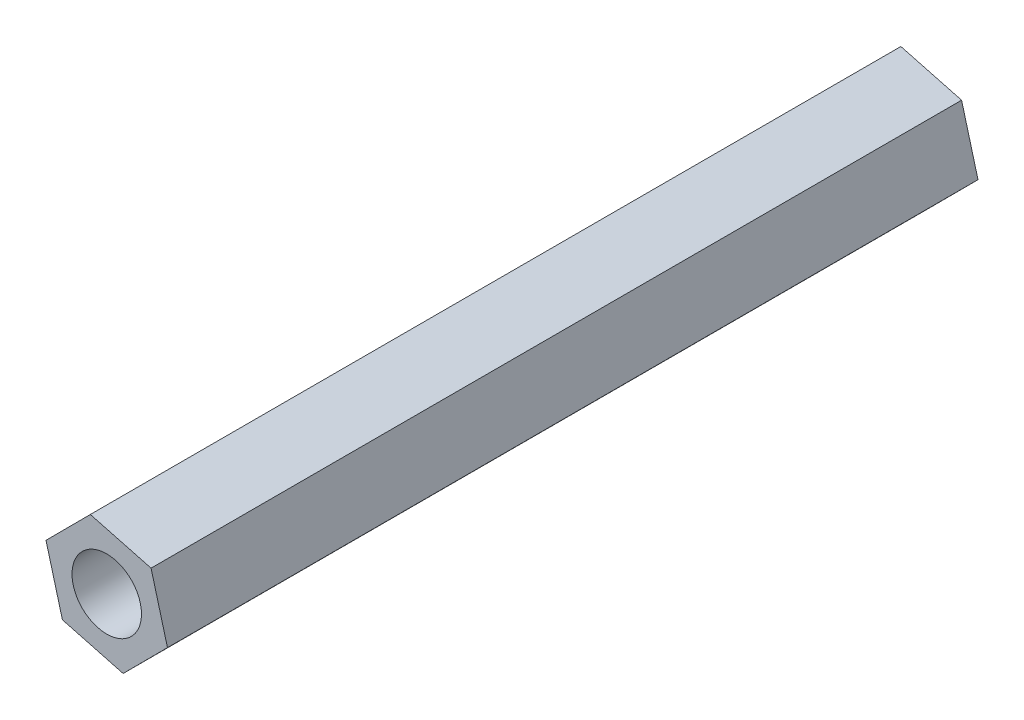
SolidWorks part; units mm, degrees
ref_plane "Front Plane" through (0, 0, 0) normal (0, 0, 1) x (1, 0, 0)
ref_plane "Top Plane" through (0, 0, 0) normal (0, 1, 0) x (1, 0, 0)
ref_plane "Right Plane" through (0, 0, 0) normal (1, 0, 0) x (0, 0, -1)
sketch "Sketch1" plane through (0, 0, 0) normal (0, 0, 1) x (1, 0, 0)
  line L1 (1.9142, 1.9233) -> (-0.7085, 2.6194)
  line L2 (-0.7085, 2.6194) -> (-2.6227, 0.6961)
  line L3 (-2.6227, 0.6961) -> (-1.9142, -1.9233)
  line L4 (-1.9142, -1.9233) -> (0.7085, -2.6194)
  line L5 (0.7085, -2.6194) -> (2.6227, -0.6961)
  line L6 (2.6227, -0.6961) -> (1.9142, 1.9233)
  circle A0 centre (0, 0) radius 2.35 construction
  circle A1 centre (0, 0) radius 1.5
  dimension "D2" = 3
  dimension "D1" = 4.7
extrude "Boss-Extrude1" add sketch "Sketch1" along normal blind 35
